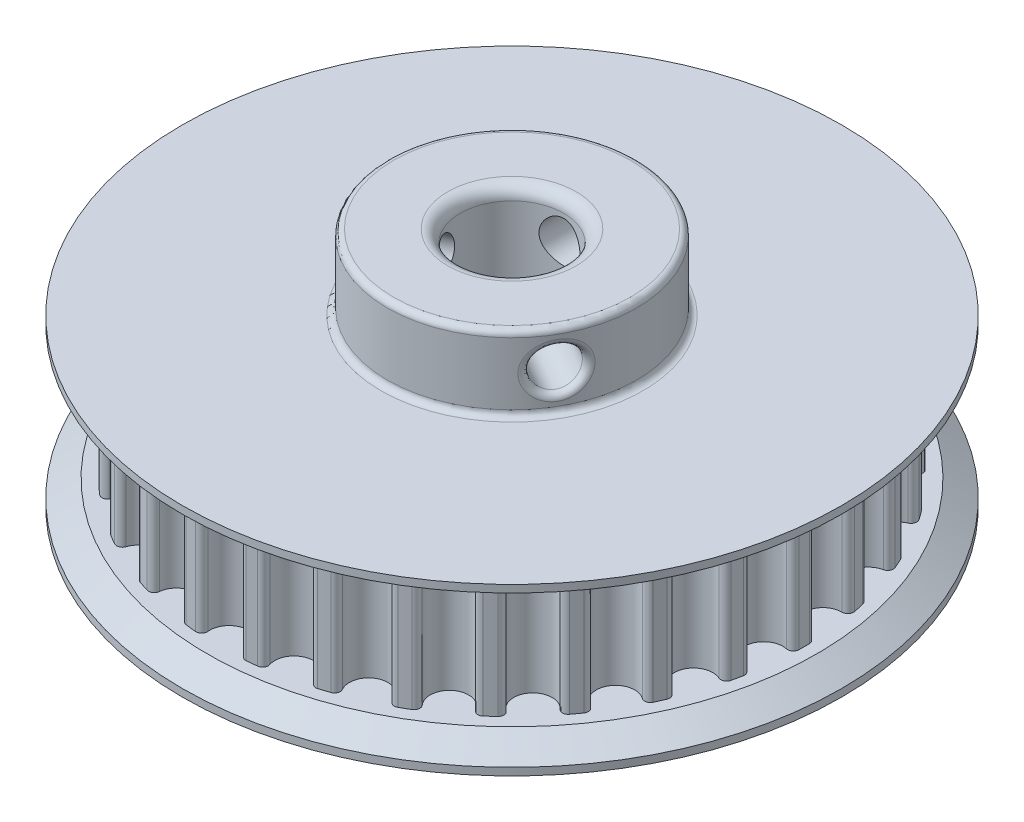
SolidWorks part; units mm, degrees
ref_plane "Plan de face" through (0, 0, 0) normal (0, 0, 1) x (1, 0, 0)
ref_plane "Plan de dessus" through (0, 0, 0) normal (0, 1, 0) x (1, 0, 0)
ref_plane "Plan de droite" through (0, 0, 0) normal (1, 0, 0) x (0, 0, -1)
sketch "Esquisse1" plane through (0, 0, 0) normal (0, 1, 0) x (1, 0, 0)
  line L0 (0, 0) -> (-2.449, 23.3007)
  line L2 (2.449, 23.3007) -> (0, 0)
  line L3 (0, 23.429) -> (0, 0) construction
  line L4 (-2.449, 23.3007) -> (2.449, 23.3007) construction
  circle A1 centre (0, 0) radius 23.429 construction
  arc A2 (-1.5343, 22.836) -> (1.5343, 22.836) centre (0, 22.672) ccw
  arc A3 (-2.449, 23.3007) -> (-2.0293, 23.341) centre (0, 0) cw
  arc A4 (-2.0293, 23.341) -> (-1.5343, 22.836) centre (-1.9897, 22.8847) cw
  arc A5 (2.449, 23.3007) -> (2.0293, 23.341) centre (0, 0) ccw
  arc A6 (2.0293, 23.341) -> (1.5343, 22.836) centre (1.9897, 22.8847) ccw
  arc A7 (-1.5343, 22.836) -> (-1.3662, 23.3892) centre (0, 22.672) cw construction
  arc A8 (1.5343, 22.836) -> (1.3662, 23.3892) centre (0, 22.672) ccw construction
  point P0 (-1.2744, 9.7605)
  point P6 (0, 21.129)
  point P20 (-0.8642, 8.7558)
  dimension "D2" = 1.543
  dimension "D3" = 0.458
  dimension "D1" = 4.898
  dimension "D4" = 2.3
  dimension "D5" = 12
extrude "Boss.-Extru.1" add sketch "Esquisse1" along normal blind 9.3
pattern_circular "Répétition circulaire1" count 30 over 360 about axis through (0, 0, 0) along (0, 1, 0) of "Boss.-Extru.1"
ref_plane "Plan1" through (0, 4.65, 0) normal (0, -1, 0) x (-1, 0, 0)
sketch "Esquisse2" plane through (0, 9.3, 0) normal (0, 1, 0) x (1, 0, 0)
  circle A0 centre (0, 0) radius 26.429
  arc A1 (22.8257, -5.2827) -> (23.001, -4.458) centre (0, 0) ccw construction
  dimension "D1" = 3
extrude "Boss.-Extru.2" add sketch "Esquisse2" along normal blind 2
mirror "Symétrie1" about plane through (0, 4.65, 0) normal (0, -1, 0) of "Boss.-Extru.2"
chamfer "Chanfrein1" distance 2 angle 35 2 edges at (0, 9.3, 26.429) (0, 0, 26.429)
sketch "Esquisse4" plane through (0, 11.3, 0) normal (0, 1, 0) x (1, 0, 0)
  circle A0 centre (0, 0) radius 10
  dimension "D1" = 20
extrude "Boss.-Extru.3" add sketch "Esquisse4" along normal blind 6
sketch "Esquisse5" plane through (0, 0, 0) normal (0, 0, 1) x (1, 0, 0)
  line L0 (0, 0) -> (0, 14.3) construction
  line L1 (10, 17.3) -> (-10, 17.3) construction
  circle A0 centre (0, 14.3) radius 1.65
  point P3 (0, 14.6319)
  dimension "D2" = 3.3
  dimension "D1" = 3
extrude "Enlèv. mat.-Extru.2" cut sketch "Esquisse5" against normal through all
pattern_circular "Répétition circulaire2" count 3 over 360 about axis through (0, 17.3, 0) along (0, -1, 0) of "Enlèv. mat.-Extru.2"
sketch "Esquisse3" plane through (0, 17.3, 0) normal (0, 1, 0) x (1, 0, 0)
  circle A0 centre (0, 0) radius 4.15
  dimension "D1" = 8.3
extrude "Enlèv. mat.-Extru.1" cut sketch "Esquisse3" against normal up to next
fillet "Congé1" radius 1 2 edges at (0, -2, -4.15) (0, 17.3, 4.15)
fillet "Congé2" radius 0.5 5 edges at (0, 11.3, 10) (0, 17.3, 10) (0.3544, 12.6885, -9.9937) (-7.7413, 13.9455, 6.3302) (9.3528, 13.9455, 3.5391)
equation "\"nb_tooth\" = 30"
equation "\"D5@Esquisse1\"=360/\"nb_tooth\""
equation "\"D1@Répétition circulaire1\"=\"nb_tooth\""
